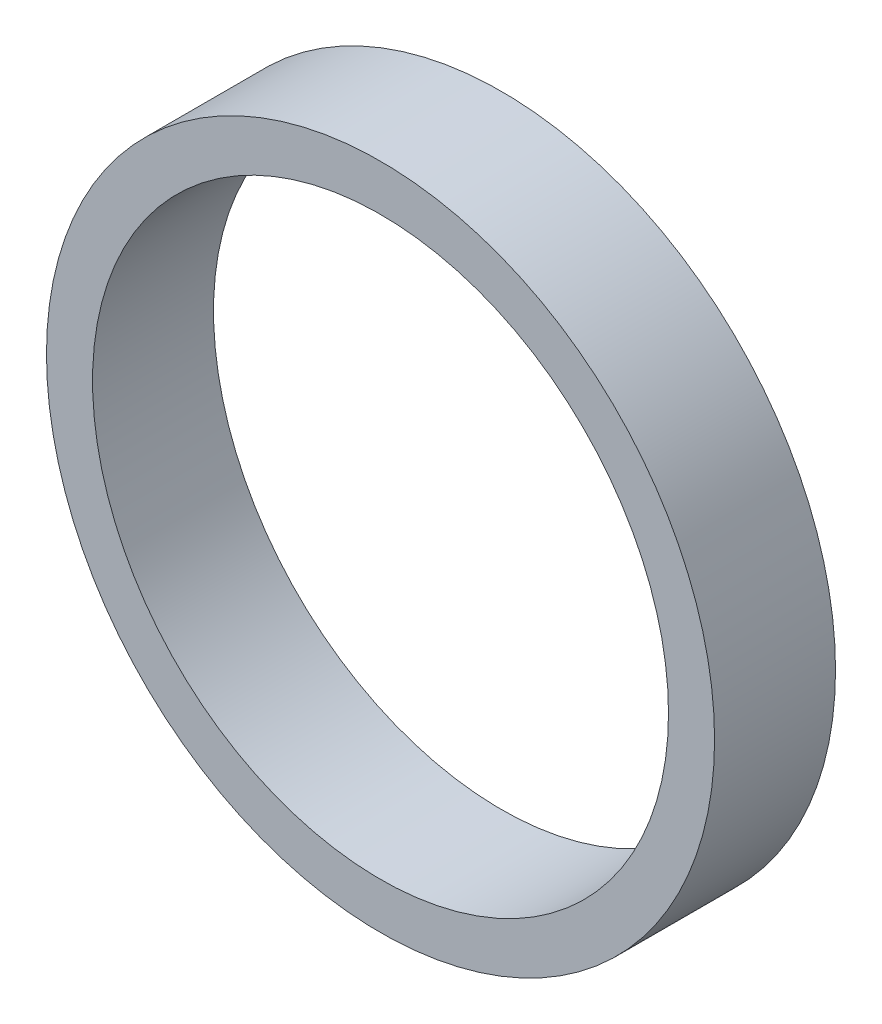
SolidWorks part; units mm, degrees
material "Alumine"
ref_plane "Plan de face" through (0, 0, 0) normal (0, 0, 1) x (1, 0, 0)
ref_plane "Plan de dessus" through (0, 0, 0) normal (0, 1, 0) x (1, 0, 0)
ref_plane "Plan de droite" through (0, 0, 0) normal (1, 0, 0) x (0, 0, -1)
sketch "Esquisse1" plane through (0, 0, 0) normal (0, 0, 1) x (1, 0, 0)
  circle A0 centre (0, 0) radius 14.5
  circle A1 centre (0, 0) radius 12.5
  dimension "D1" = 25
  dimension "D2" = 29
extrude "Boss.-Extru.1" add sketch "Esquisse1" along normal blind 5.25
